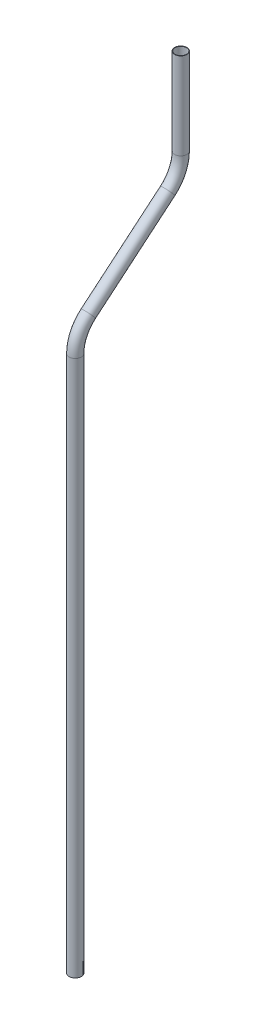
SolidWorks part; units mm, degrees
ref_plane "Front Plane" through (0, 0, 0) normal (0, 0, 1) x (1, 0, 0)
ref_plane "Top Plane" through (0, 0, 0) normal (0, 1, 0) x (1, 0, 0)
ref_plane "Right Plane" through (0, 0, 0) normal (1, 0, 0) x (0, 0, -1)
sketch "Sketch1" plane through (0, 0, 0) normal (0, 1, 0) x (1, 0, 0)
  circle A0 centre (0, 0) radius 6.35
  circle A1 centre (0, 0) radius 5.969
  dimension "D1" = 12.7
  dimension "D2" = 11.938
sketch "Sketch2" plane through (0, 0, 0) normal (1, 0, 0) x (0, 0, -1)
  line L0 (0, 0) -> (0, 558.8)
  line L1 (13.6098, 587.9863) -> (96.3043, 657.3752)
  line L2 (109.9141, 686.5615) -> (109.9141, 776.7315)
  arc A0 (0, 558.8) -> (13.6098, 587.9863) centre (38.1, 558.8) cw
  arc A1 (96.3043, 657.3752) -> (109.9141, 686.5615) centre (71.8141, 686.5615) ccw
  dimension "D3" = 38.1
  dimension "D5" = 38.1
  dimension "D1" = 558.8
  dimension "D2" = 130
  dimension "D4" = 130
  dimension "D6" = 90.17
  dimension "D7" = 107.95
sweep "Sweep2" add profiles "Sketch1" path "Sketch2"
